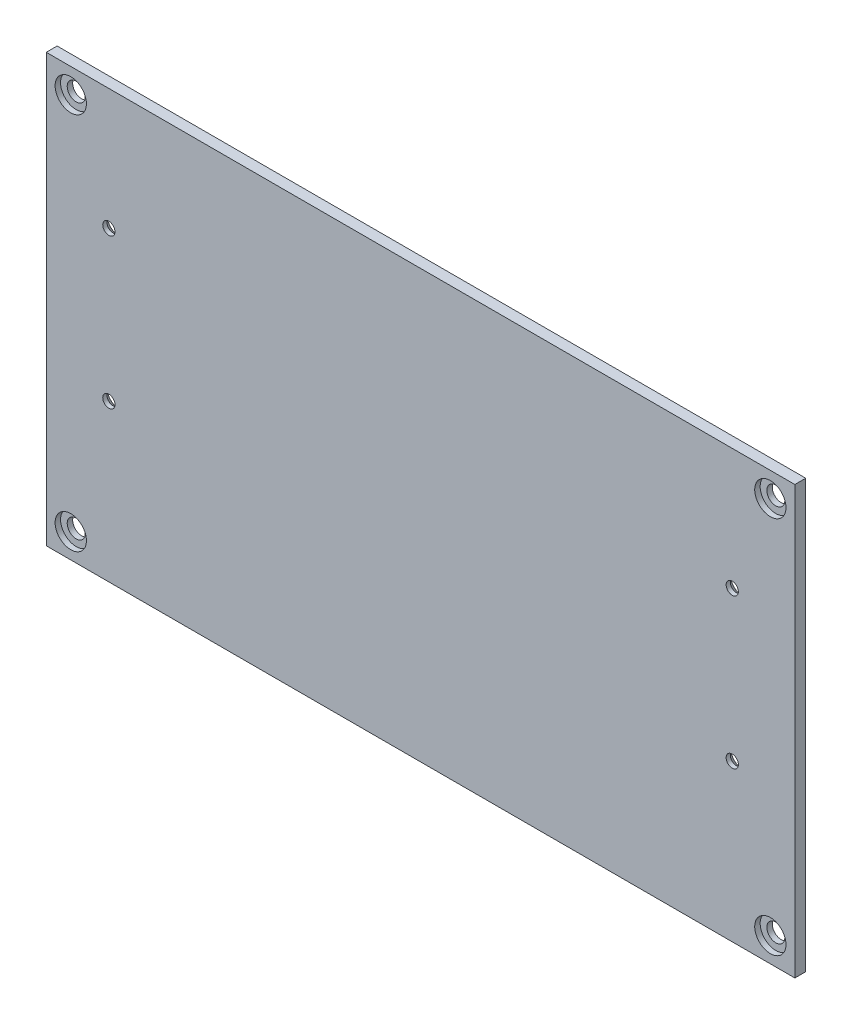
SolidWorks part; units mm, degrees
ref_plane "Plan de face" through (0, 0, 0) normal (0, 0, 1) x (1, 0, 0)
ref_plane "Plan de dessus" through (0, 0, 0) normal (0, 1, 0) x (1, 0, 0)
ref_plane "Plan de droite" through (0, 0, 0) normal (1, 0, 0) x (0, 0, -1)
sketch "Esquisse4" plane through (0, 0, 0) normal (0, 0, 1) x (1, 0, 0)
  line L0 (-137.5, 78.5) -> (-137.5, -78.5)
  line L1 (-137.5, -78.5) -> (137.5, -78.5)
  line L2 (0, -55) -> (0, 55) construction
  line L3 (137.5, 78.5) -> (137.5, -78.5)
  line L4 (55, 0) -> (-55, 0) construction
  line L5 (-137.5, 78.5) -> (137.5, 78.5)
  dimension "D1" = 157
  dimension "D2" = 275
extrude "Boss.-Extru.2" add sketch "Esquisse4" along normal blind 4
sketch "Esquisse5" plane through (0, 0, 0) normal (0, 0, -1) x (-1, 0, 0)
  line L0 (-114.5, 78.5) -> (-114.5, -78.5) construction
  line L1 (-137.5, 78.5) -> (137.5, 78.5) construction
  line L2 (137.5, -78.5) -> (-137.5, -78.5) construction
  line L3 (-137.5, -78.5) -> (-137.5, 78.5) construction
  line L4 (0, 2.2) -> (0, -2.2) construction
  point P8 (-114.5, 34)
  point P9 (-114.5, -21)
  point P12 (114.5, 34)
  point P13 (114.5, -21)
  dimension "D1" = 23
  dimension "D2" = 44.5
  dimension "D3" = 57.5
hole_wizard "Fraisage pour vis à tête fraisée M42" positions "Esquisse5" profile "Esquisse6" countersink size "M4" standard "Ansi Metric" end condition through all
sketch "Esquisse6" plane through (-114.5, -21, 0) normal (1, 0, 0) x (0, 1, 0)
  line L0 (0, 0) -> (0, 4)
  line L1 (0, 4) -> (2.25, 4)
  line L2 (2.25, 4) -> (2.25, 2.45)
  line L3 (2.25, 2.45) -> (4.7, 0)
  line L5 (4.7, 0) -> (0, 0)
  line L6 (-2.25, 2.45) -> (-4.7, 0) construction
  line L11 (0, -6.35) -> (0, 107.95) construction
  dimension "Diamètre du perçage jusqu'au prochain" = 4.5
  dimension "Profondeur du perçage jusqu'au prochain" = 4
  dimension "Diamètre du fraisage entrant" = 9.4
  dimension "Angle du fraisage entrant" = 90
sketch "Esquisse7" plane through (0, 0, 4) normal (0, 0, 1) x (1, 0, 0)
  line L0 (-137.5, -69.5) -> (-128.5, -69.5) construction
  line L1 (-137.5, 78.5) -> (-137.5, -78.5) construction
  line L2 (-128.5, -69.5) -> (-128.5, -78.5) construction
  line L3 (-137.5, -78.5) -> (137.5, -78.5) construction
  line L4 (2.2, 0) -> (-2.2, 0) construction
  line L5 (0, -2.2) -> (0, 2.2) construction
  point P8 (-128.5, -69.5)
  point P10 (-128.5, 69.5)
  point P14 (128.5, 69.5)
  point P15 (128.5, -69.5)
  dimension "D1" = 9
  dimension "D2" = 9
hole_wizard "Chambrage pour Vis à tête ronde à 6 pans creux M61" positions "Esquisse7" profile "Esquisse8" counterbore size "M6" standard "Ansi Metric" end condition through all
sketch "Esquisse8" plane through (128.5, -69.5, 4) normal (1, 0, 0) x (0, -1, 0)
  line L0 (0, 0) -> (0, 4)
  line L1 (0, 4) -> (3.3, 4)
  line L3 (3.3, 4) -> (3.3, 2)
  line L4 (3.3, 2) -> (5.75, 2)
  line L5 (5.75, 2) -> (5.75, 0)
  line L7 (5.75, 0) -> (0, 0)
  line L11 (0, -6.35) -> (0, 107.95) construction
  dimension "Diamètre du perçage jusqu'au prochain" = 6.6
  dimension "Profondeur du perçage jusqu'au prochain" = 4
  dimension "Diamètre du chambrage" = 11.5
  dimension "Profondeur du chambrage" = 2
